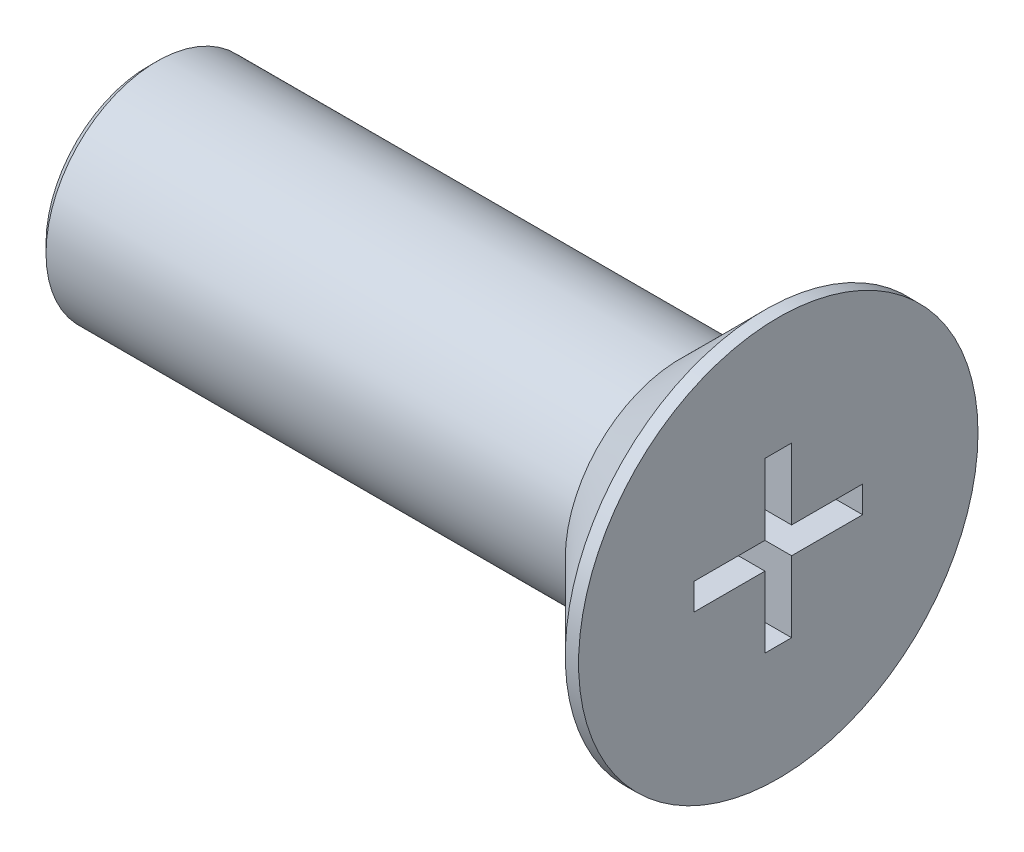
SolidWorks part; units mm, degrees
ref_plane "前视基准面" through (0, 0, 0) normal (0, 0, 1) x (1, 0, 0)
ref_plane "上视基准面" through (0, 0, 0) normal (0, 1, 0) x (1, 0, 0)
ref_plane "右视基准面" through (0, 0, 0) normal (1, 0, 0) x (0, 0, -1)
sketch "草图1" plane through (0, 0, 0) normal (1, 0, 0) x (0, 0, -1)
  circle A0 centre (0, 0) radius 4.5
  dimension "D1" = 9
extrude "凸台-拉伸1" add sketch "草图1" along normal blind 2.2
sketch "草图2" plane through (0, 0, 0) normal (-1, 0, 0) x (0, 0, 1)
  circle A0 centre (0, 0) radius 2.5
  dimension "D1" = 5
extrude "凸台-拉伸3" add sketch "草图2" along normal blind 12
cosmetic thread "装饰螺纹线1" parameters "D2"=4
chamfer "倒角2" distance 0.2 angle 45 1 edges at (-12, 0, 2.5)
chamfer "倒角3" distance 1.9 angle 45 1 edges at (0, 0, -4.5)
sketch "草图5" plane through (2.2, 0, 0) normal (1, 0, 0) x (0, 0, -1)
  line L0 (0.3, 0.3) -> (1.9, 0.3)
  line L1 (1.9, 0.3) -> (1.9, -0.3)
  line L2 (1.9, -0.3) -> (0.3, -0.3)
  line L3 (0.3, -0.3) -> (0.3, -1.9)
  line L4 (0.3, -1.9) -> (-0.3, -1.9)
  line L5 (-0.3, -1.9) -> (-0.3, -0.3)
  line L6 (-0.3, -0.3) -> (-1.9, -0.3)
  line L7 (-1.9, -0.3) -> (-1.9, 0.3)
  line L8 (-1.9, 0.3) -> (-0.3, 0.3)
  line L9 (-0.3, 0.3) -> (-0.3, 1.9)
  line L10 (-0.3, 1.9) -> (0.3, 1.9)
  line L11 (0.3, 1.9) -> (0.3, 0.3)
  dimension "D1" = 0.6
  dimension "D2" = 0.6
  dimension "D3" = 0.6
  dimension "D4" = 0.6
  dimension "D5" = 0.3
  dimension "D6" = 0.3
  dimension "D7" = 0.3
  dimension "D8" = 0.3
  dimension "D9" = 1.6
  dimension "D10" = 1.6
  dimension "D11" = 1.6
  dimension "D12" = 1.6
extrude "切除-拉伸2" cut sketch "草图5" against normal blind 3
